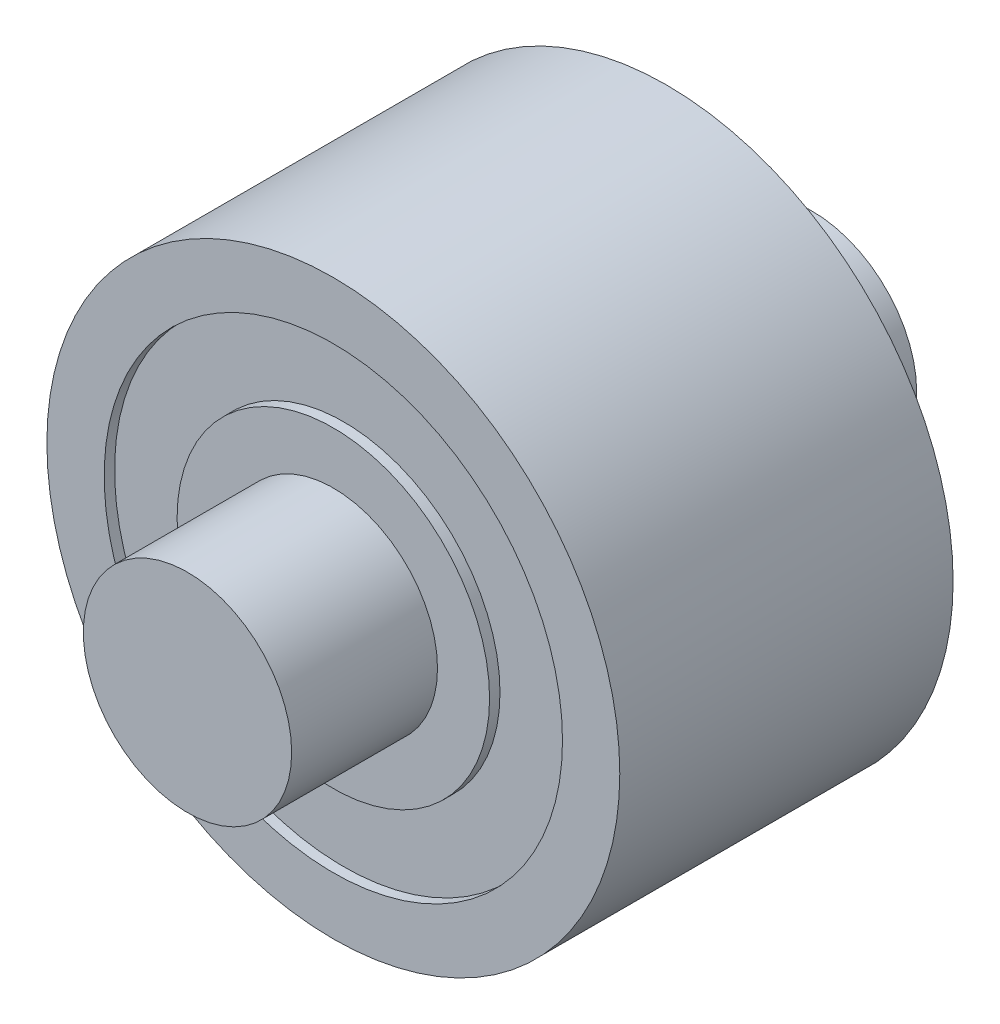
SolidWorks part; units mm, degrees
ref_plane "Alzado" through (0, 0, 0) normal (0, 0, 1) x (1, 0, 0)
ref_plane "Planta" through (0, 0, 0) normal (0, 1, 0) x (1, 0, 0)
ref_plane "Vista lateral" through (0, 0, 0) normal (1, 0, 0) x (0, 0, -1)
sketch "Croquis1" plane through (0, 0, 0) normal (0, 0, 1) x (1, 0, 0)
  circle A0 centre (0, 0) radius 11
extrude "Saliente-Extruir1" add sketch "Croquis1" along normal blind 12.8
sketch "Croquis2" plane through (0, 0, 12.8) normal (0, 0, 1) x (1, 0, 0)
  circle A0 centre (0, 0) radius 8.8
  circle A1 centre (0, 0) radius 6
  dimension "D1" = 17.6
  dimension "D2" = 12
extrude "Cortar-Extruir1" cut sketch "Croquis2" against normal blind 0.4
sketch "Croquis3" plane through (0, 0, 12.8) normal (0, 0, 1) x (1, 0, 0)
  circle A0 centre (0, 0) radius 4
extrude "Saliente-Extruir2" add sketch "Croquis3" along normal blind 5.6
ref_plane "Plano1" through (0, 0, 6.4) normal (0, 0, 1) x (1, 0, 0)
mirror "Simetría1" about plane through (0, 0, 6.4) normal (0, 0, 1) of "Saliente-Extruir2", "Cortar-Extruir1"
